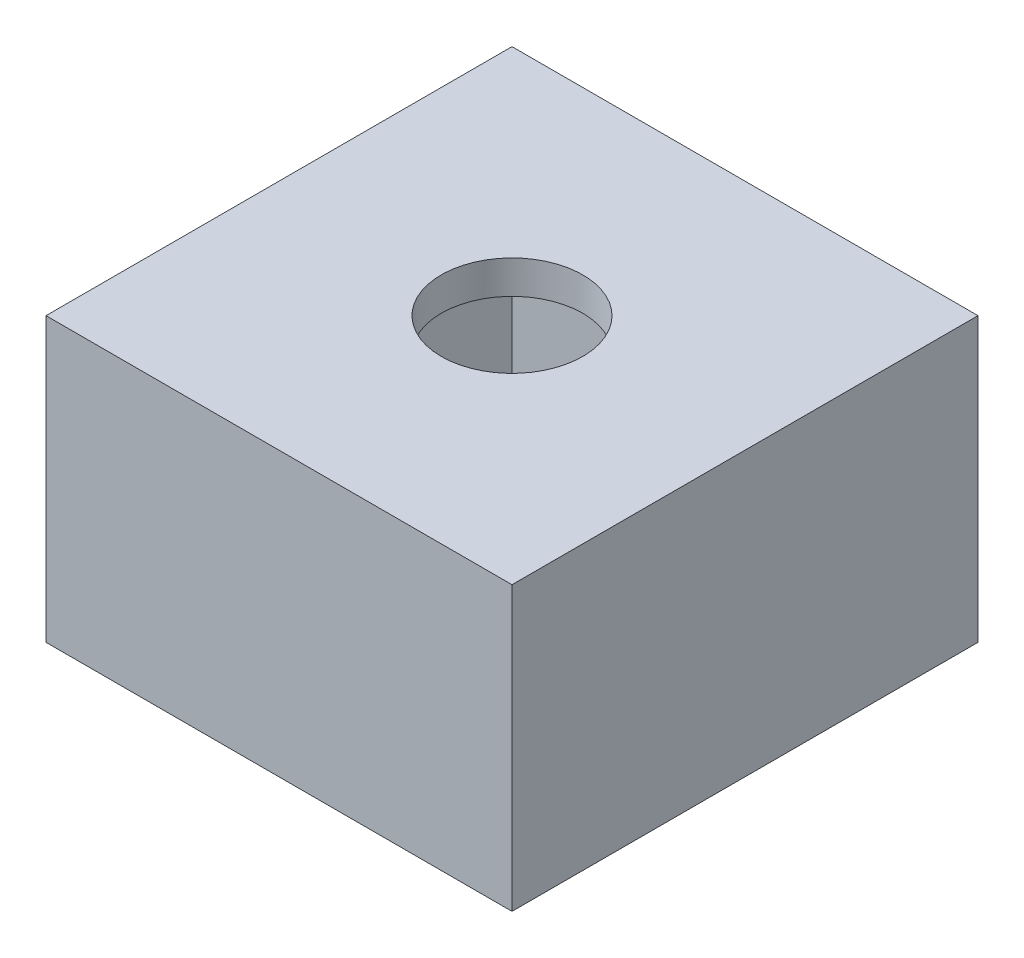
SolidWorks part; units mm, degrees
ref_plane "Front Plane" through (0, 0, 0) normal (0, 0, 1) x (1, 0, 0)
ref_plane "Top Plane" through (0, 0, 0) normal (0, 1, 0) x (1, 0, 0)
ref_plane "Right Plane" through (0, 0, 0) normal (1, 0, 0) x (0, 0, -1)
sketch "Sketch1" plane through (0, 0, 0) normal (0, 1, 0) x (1, 0, 0)
  line L0 (14, 14) -> (-14, 14)
  line L1 (12, -12) -> (-12, -12)
  line L2 (12, -12) -> (12, 12)
  line L3 (12, 12) -> (-12, 12)
  line L4 (-12, -12) -> (-12, 12)
  line L5 (12, -12) -> (-12, 12) construction
  line L6 (12, 12) -> (-12, -12) construction
  line L7 (-14, -14) -> (-14, 14)
  line L8 (14, -14) -> (-14, -14)
  line L9 (14, -14) -> (14, 14)
  point P0 (0, 0)
  dimension "D1" = 24
  dimension "D2" = 2
extrude "Boss-Extrude1" add sketch "Sketch1" along normal blind 15
sketch "Sketch2" plane through (0, 15, 0) normal (0, 1, 0) x (1, 0, 0)
  line L1 (-14, -14) -> (14, -14)
  line L2 (-14, -14) -> (-14, 14)
  line L3 (-14, 14) -> (14, 14)
  line L4 (14, -14) -> (14, 14)
  line L5 (-14, -14) -> (14, 14) construction
  line L6 (-14, 14) -> (14, -14) construction
  point P0 (0, 0)
extrude "Boss-Extrude2" add sketch "Sketch2" along normal blind 2
sketch "Sketch3" plane through (0, 17, 0) normal (0, 1, 0) x (1, 0, 0)
  circle A0 centre (0, 0) radius 4.25
  dimension "D1" = 8.5
extrude "Cut-Extrude1" cut sketch "Sketch3" against normal up to next
